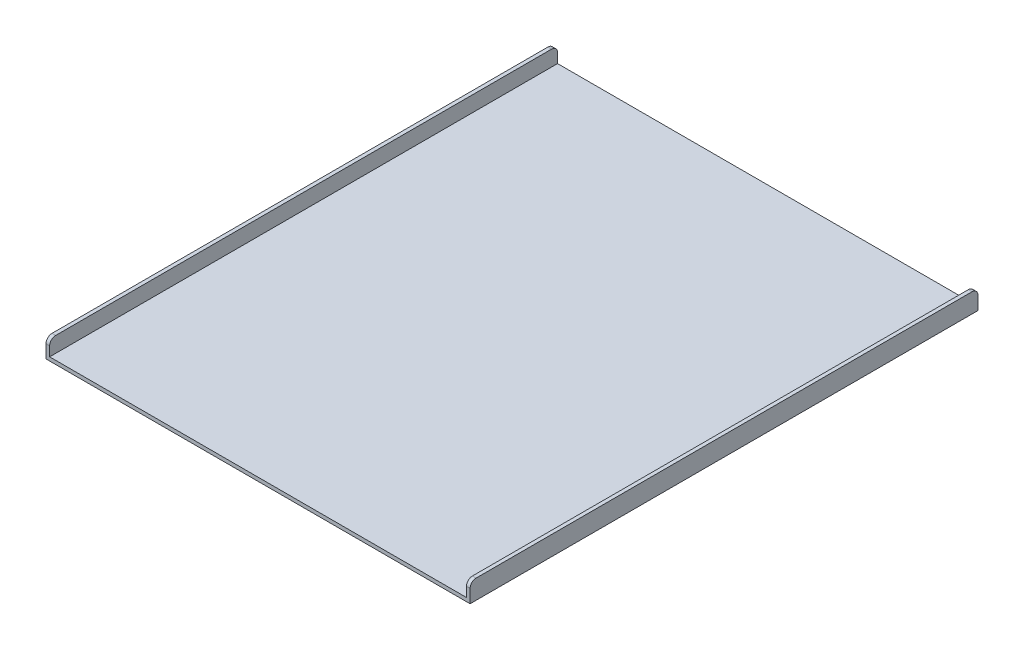
SolidWorks part; units mm, degrees
ref_plane "Front Plane" through (0, 0, 0) normal (0, 0, 1) x (1, 0, 0)
ref_plane "Top Plane" through (0, 0, 0) normal (0, 1, 0) x (1, 0, 0)
ref_plane "Right Plane" through (0, 0, 0) normal (1, 0, 0) x (0, 0, -1)
sketch "Sketch1" plane through (0, 0, 0) normal (0, 0, 1) x (1, 0, 0)
  line L0 (-250.5141, 25.7536) -> (-250.5141, 0)
  line L1 (-250.5141, 0) -> (440.5033, 0)
  line L2 (440.5033, 0) -> (440.5033, 25.9157)
  dimension "D1" = 691.0174
  dimension "D2" = 250.5141
  dimension "D3" = 25.7536
  dimension "D4" = 25.9157
extrude "Extrude-Thin1" add sketch "Sketch1" along normal mid plane 842.0984 thin
sketch "Sketch3" plane through (446.5515, 0, 0) normal (1, 0, 0) x (0, 0, -1)
  line L0 (-300, 23.9518) -> (0, 23.9518) construction
  line L1 (-300, 28.9518) -> (0, 28.9518)
  line L2 (-300, 18.9518) -> (0, 18.9518)
  line L3 (-421.0492, -6.0482) -> (421.0492, -6.0482) construction
  line L4 (421.0492, -6.0482) -> (421.0492, 25.9157) construction
  circle A0 centre (391.0492, 23.9518) radius 5
  arc A1 (-300, 28.9518) -> (-300, 18.9518) centre (-300, 23.9518) ccw
  arc A2 (0, 18.9518) -> (0, 28.9518) centre (0, 23.9518) ccw
  point P4 (-150, 23.9518)
  dimension "D1" = 10
  dimension "D2" = 30
  dimension "D3" = 30
  dimension "D4" = 150
  dimension "D5" = 300
  dimension "D6" = 10
fillet "Fillet1" radius 10 4 edges at (-253.5382, 25.7536, -421.0492) (443.5274, 25.9157, -421.0492) (443.5274, 25.9157, 421.0492) (-253.5382, 25.7536, 421.0492)
sketch "草图2" plane through (0, -6.0482, 0) normal (0, -1, 0) x (-1, 0, 0)
  circle A0 centre (-360.1647, 358.0127) radius 19.05
extrude "凸台-拉伸1" add sketch "草图2" along normal blind 23.2497 contours A0
sketch "草图3" plane through (0, -6.0482, 0) normal (0, -1, 0) x (-1, 0, 0)
  circle A0 centre (174.0605, -351.2742) radius 19.05
extrude "凸台-拉伸2" add sketch "草图3" along normal blind 23 contours A0
sketch "草图5" plane through (0, -29.2979, 0) normal (0, -1, 0) x (-1, 0, 0)
  line L0 (-414.0127, 358.0146) -> (-414.0685, -1165.9854)
  line L1 (-306.3167, 358.0107) -> (-306.3725, -1165.9893)
  arc A2 (-306.3167, 358.0107) -> (-414.0127, 358.0146) centre (-360.1647, 358.0127) ccw
sketch "草图7" plane through (0, -29.0482, 0) normal (0, -1, 0) x (-1, 0, 0)
  line L0 (173.269, -297.432) -> (667.9577, -290.1602)
  line L1 (136.6985, -390.0516) -> (933.7243, -1157.9865)
  arc A0 (173.269, -297.432) -> (136.6985, -390.0516) centre (174.0605, -351.2742) ccw
